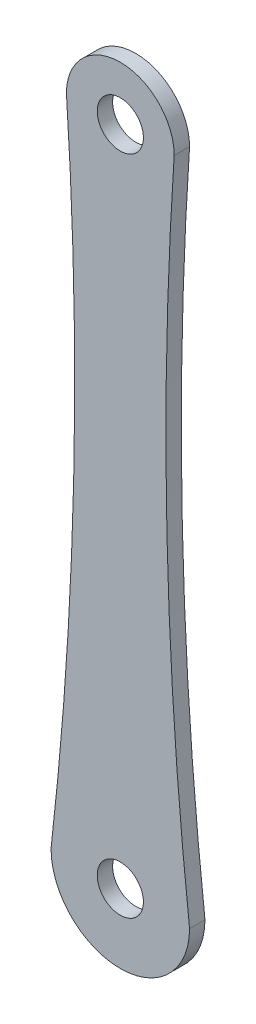
SolidWorks part; units mm, degrees
ref_plane "Alzado" through (0, 0, 0) normal (0, 0, 1) x (1, 0, 0)
ref_plane "Planta" through (0, 0, 0) normal (0, 1, 0) x (1, 0, 0)
ref_plane "Vista lateral" through (0, 0, 0) normal (1, 0, 0) x (0, 0, -1)
sketch "Croquis2" plane through (0, 0, 0) normal (0, 0, 1) x (1, 0, 0)
  line L0 (0, 0) -> (0, 51) construction
  line L1 (11.9309, 49) -> (-14.9247, 49) construction
  line L2 (-13.4066, 4.5) -> (14.5424, 4.5) construction
  line L3 (11.9309, 47.5) -> (-14.2871, 47.5) construction
  line L5 (-13.4066, 3) -> (14.5424, 3) construction
  arc A0 (3.5, 47.5) -> (-3.5, 47.5) centre (0, 47.5) ccw
  circle A1 centre (0, 47.5) radius 1.5
  arc A2 (-4.5, 4.5) -> (4.5, 4.5) centre (0, 4.5) ccw
  circle A3 centre (0, 4.5) radius 1.5
  arc A4 (-3.5, 47.5) -> (-4.5, 4.5) centre (-241.5679, 31.5248) cw
  arc A5 (3.5, 47.5) -> (4.5, 4.5) centre (241.5679, 31.5248) ccw
extrude "Saliente-Extruir1" add sketch "Croquis2" along normal blind 1
scale "Escala1" scale about centroid uniform scaling yes scale factor 7
